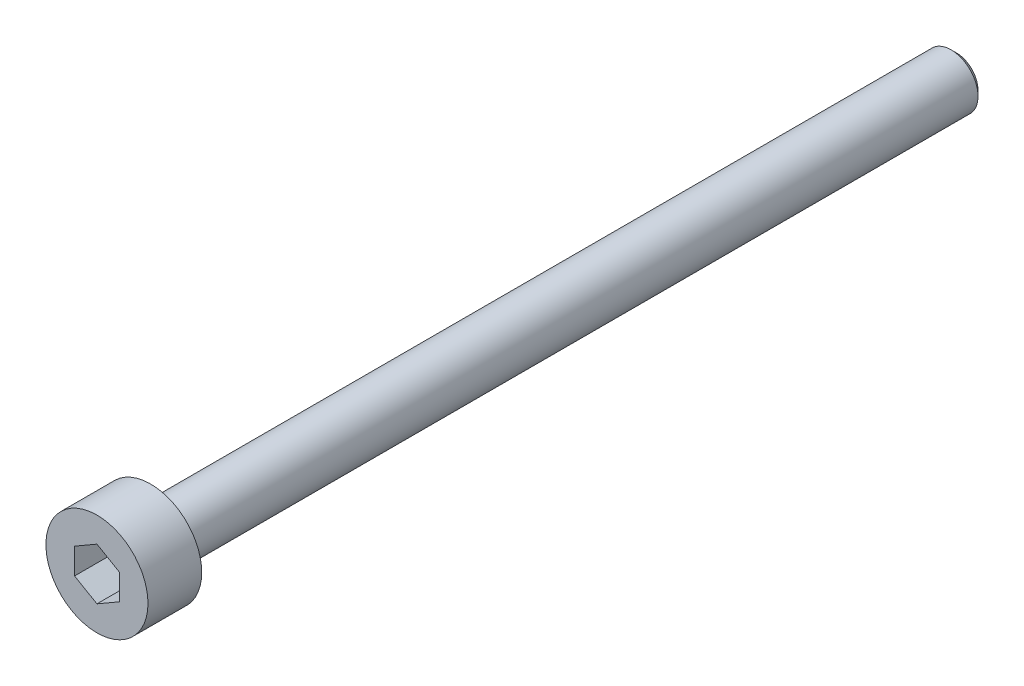
SolidWorks part; units mm, degrees
ref_plane "Front Plane" through (0, 0, 0) normal (0, 0, 1) x (1, 0, 0)
ref_plane "Top Plane" through (0, 0, 0) normal (0, 1, 0) x (1, 0, 0)
ref_plane "Right Plane" through (0, 0, 0) normal (1, 0, 0) x (0, 0, -1)
sketch "Sketch1" plane through (0, 0, 0) normal (0, 0, 1) x (1, 0, 0)
  circle A0 centre (0, 0) radius 2.85
  dimension "D1" = 5.7
extrude "Boss-Extrude1" add sketch "Sketch1" along normal blind 3
sketch "Sketch2" plane through (0, 0, 0) normal (0, 0, -1) x (-1, 0, 0)
  circle A0 centre (0, 0) radius 1.5
  dimension "D1" = 3
extrude "Boss-Extrude2" add sketch "Sketch2" along normal blind 45
chamfer "Chamfer1" distance 0.3 angle 45 1 edges at (-1.5, 0, -45)
sketch "Sketch3" plane through (0, 0, 3) normal (0, 0, 1) x (1, 0, 0)
  line L1 (0, 1.4434) -> (-1.25, 0.7217)
  line L2 (-1.25, 0.7217) -> (-1.25, -0.7217)
  line L3 (-1.25, -0.7217) -> (0, -1.4434)
  line L4 (0, -1.4434) -> (1.25, -0.7217)
  line L5 (1.25, -0.7217) -> (1.25, 0.7217)
  line L6 (1.25, 0.7217) -> (0, 1.4434)
  circle A0 centre (0, 0) radius 1.25 construction
  dimension "D1" = 2.5
extrude "Cut-Extrude1" cut sketch "Sketch3" against normal blind 2
